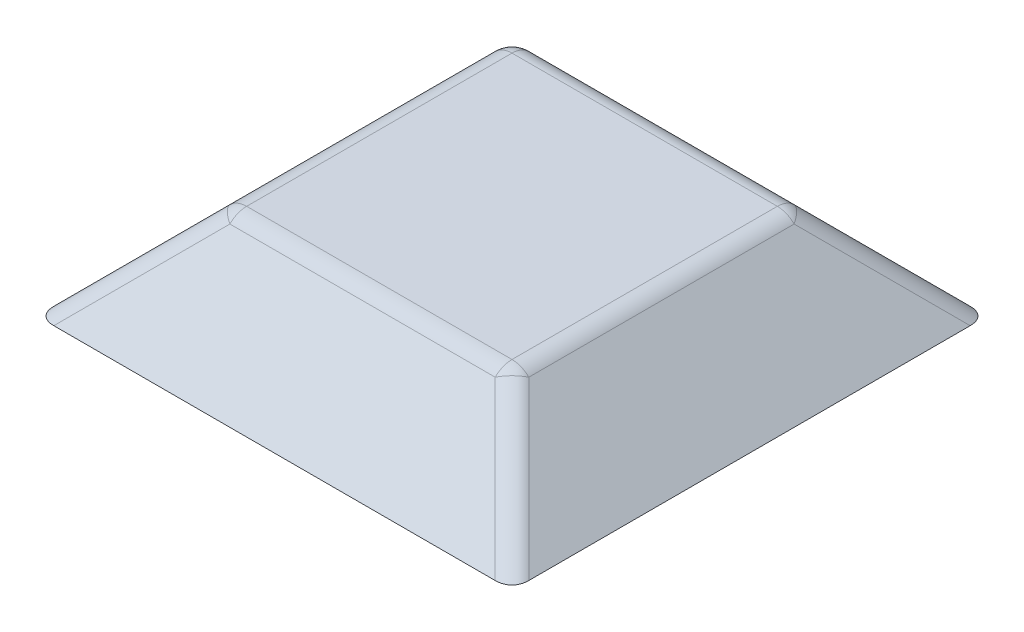
SolidWorks part; units mm, degrees
ref_plane "Front Plane" through (0, 0, 0) normal (0, 0, 1) x (1, 0, 0)
ref_plane "Top Plane" through (0, 0, 0) normal (0, 1, 0) x (1, 0, 0)
ref_plane "Right Plane" through (0, 0, 0) normal (1, 0, 0) x (0, 0, -1)
sketch "Croquis1" plane through (0, 0, 0) normal (0, 1, 0) x (1, 0, 0)
  line L1 (5, -5) -> (-5, -5)
  line L2 (5, -5) -> (5, 5)
  line L3 (5, 5) -> (-5, 5)
  line L4 (-5, -5) -> (-5, 5)
  line L5 (5, -5) -> (-5, 5) construction
  line L6 (5, 5) -> (-5, -5) construction
  point P0 (0, 0)
  dimension "D1" = 10
  dimension "D2" = 10
extrude "Saliente-Extruir1" add sketch "Croquis1" along normal blind 2 draft 45
fillet "Redondeo1" radius 0.5 8 edges at (0, 2, -3) (3, 2, 0) (4, 1, -4) (4, 1, 4) (-4, 1, 4) (-4, 1, -4) (-3, 2, 0) (0, 2, 3)
sketch "Croquis2" plane through (0, 0, 0) normal (0, -1, 0) x (1, 0, 0)
  line L0 (4.6464, -5) -> (-4.6464, -5) construction
  line L1 (5, 4.6464) -> (5, -4.6464) construction
  line L2 (-4.6464, 5) -> (4.6464, 5) construction
  line L3 (-5, -4.6464) -> (-5, 4.6464) construction
  line L4 (4.6464, -5) -> (-4.6464, -5)
  line L5 (5, 4.6464) -> (5, -4.6464)
  line L6 (-4.6464, 5) -> (4.6464, 5)
  line L7 (-5, -4.6464) -> (-5, 4.6464)
  ellipse E0 centre (-4.2929, -4.2929) end of major axis (-4.9053, -4.9053) minor radius 0.5 (-5, -4.6464) -> (-4.6464, -5) ccw construction
  ellipse E1 centre (4.2929, -4.2929) end of major axis (4.9053, -4.9053) minor radius 0.5 (4.6464, -5) -> (5, -4.6464) ccw construction
  ellipse E2 centre (4.2929, 4.2929) end of major axis (4.9053, 4.9053) minor radius 0.5 (5, 4.6464) -> (4.6464, 5) ccw construction
  ellipse E3 centre (-4.2929, 4.2929) end of major axis (-4.9053, 4.9053) minor radius 0.5 (-4.6464, 5) -> (-5, 4.6464) ccw construction
  ellipse E4 centre (-4.2929, -4.2929) end of major axis (-4.9053, -4.9053) minor radius 0.5 (-5, -4.6464) -> (-4.6464, -5) ccw
  ellipse E5 centre (4.2929, -4.2929) end of major axis (4.9053, -4.9053) minor radius 0.5 (4.6464, -5) -> (5, -4.6464) ccw
  ellipse E6 centre (4.2929, 4.2929) end of major axis (4.9053, 4.9053) minor radius 0.5 (5, 4.6464) -> (4.6464, 5) ccw
  ellipse E7 centre (-4.2929, 4.2929) end of major axis (-4.9053, 4.9053) minor radius 0.5 (-4.6464, 5) -> (-5, 4.6464) ccw
